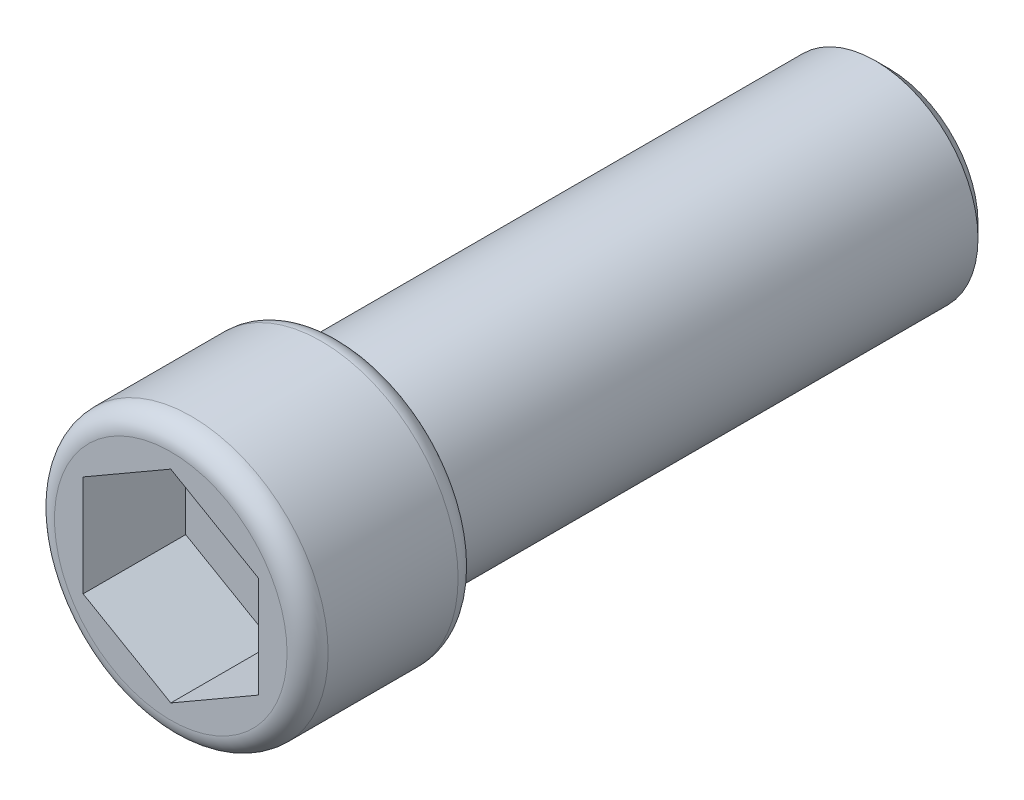
SolidWorks part; units mm, degrees
ref_plane "前视基准面" through (0, 0, 0) normal (0, 0, 1) x (1, 0, 0)
ref_plane "上视基准面" through (0, 0, 0) normal (0, 1, 0) x (1, 0, 0)
ref_plane "右视基准面" through (0, 0, 0) normal (1, 0, 0) x (0, 0, -1)
sketch "草图1" plane through (0, 0, 0) normal (0, 0, 1) x (1, 0, 0)
  circle A0 centre (0, 0) radius 1.5
extrude "凸台-拉伸1" add sketch "草图1" along normal blind 8
sketch "草图2" plane through (0, 0, 8) normal (0, 0, 1) x (1, 0, 0)
  circle A0 centre (0, 0) radius 2
extrude "凸台-拉伸2" add sketch "草图2" along normal blind 2.5
sketch "草图3" plane through (0, 0, 10.5) normal (0, 0, 1) x (1, 0, 0)
  line L1 (0, 1.4801) -> (-1.2818, 0.74)
  line L2 (-1.2818, 0.74) -> (-1.2818, -0.74)
  line L3 (-1.2818, -0.74) -> (0, -1.4801)
  line L4 (0, -1.4801) -> (1.2818, -0.74)
  line L5 (1.2818, -0.74) -> (1.2818, 0.74)
  line L6 (1.2818, 0.74) -> (0, 1.4801)
  circle A0 centre (0, 0) radius 1.2818 construction
extrude "切除-拉伸1" cut sketch "草图3" against normal blind 1.5
fillet "圆角1" radius 0.3 2 edges at (2, 0, 8) (2, 0, 10.5)
chamfer "倒角1" distance 0.2 angle 45 1 edges at (1.5, 0, 0)
